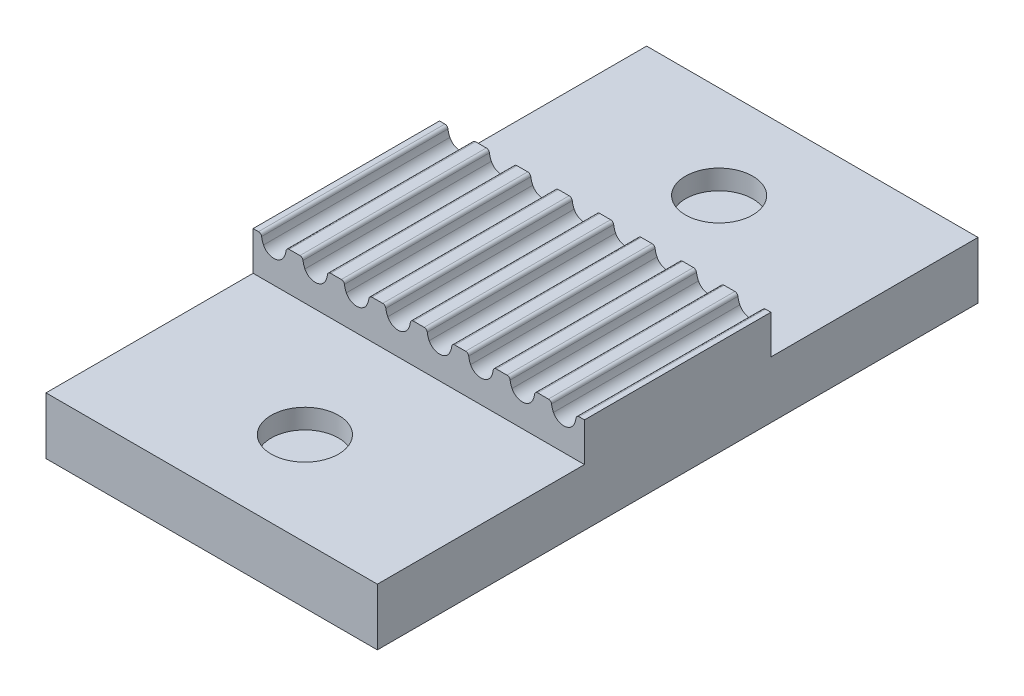
SolidWorks part; units mm, degrees
ref_plane "Front Plane" through (0, 0, 0) normal (0, 0, 1) x (1, 0, 0)
ref_plane "Top Plane" through (0, 0, 0) normal (0, 1, 0) x (1, 0, 0)
ref_plane "Right Plane" through (0, 0, 0) normal (1, 0, 0) x (0, 0, -1)
sketch "Sketch1" plane through (0, 0, 0) normal (0, 0, 1) x (1, 0, 0)
  line L0 (16.338, 17.8213) -> (16.5978, 17.8213)
  line L1 (12.338, 17.8213) -> (12.8577, 17.8213)
  line L2 (14.338, 17.8213) -> (14.8577, 17.8213)
  line L3 (8.338, 17.8213) -> (8.8577, 17.8213)
  line L4 (10.338, 17.8213) -> (10.8577, 17.8213)
  line L5 (16.5978, 17.8213) -> (16.5978, 15.9513)
  line L6 (0.5978, 17.8213) -> (0.5978, 15.9513)
  line L7 (4.338, 17.8213) -> (4.8577, 17.8213)
  line L8 (6.338, 17.8213) -> (6.8577, 17.8213)
  line L9 (0.5978, 17.8213) -> (0.8577, 17.8213)
  line L10 (2.338, 17.8213) -> (2.8577, 17.8213)
  line L11 (0.5978, 15.9513) -> (16.5978, 15.9513)
  arc A0 (15.5978, 17.0713) -> (16.0967, 17.3831) centre (15.5978, 17.6263) ccw
  arc A1 (16.0967, 17.3831) -> (16.1893, 17.6909) centre (15.1978, 17.8213) ccw
  arc A2 (16.338, 17.8213) -> (16.1893, 17.6909) centre (16.338, 17.6713) ccw
  arc A3 (13.099, 17.3831) -> (13.5978, 17.0713) centre (13.5978, 17.6263) ccw
  arc A4 (13.0064, 17.6909) -> (13.099, 17.3831) centre (13.9978, 17.8213) ccw
  arc A5 (13.0064, 17.6909) -> (12.8577, 17.8213) centre (12.8577, 17.6713) ccw
  arc A6 (11.5978, 17.0713) -> (12.0967, 17.3831) centre (11.5978, 17.6263) ccw
  arc A7 (12.0967, 17.3831) -> (12.1893, 17.6909) centre (11.1978, 17.8213) ccw
  arc A8 (12.338, 17.8213) -> (12.1893, 17.6909) centre (12.338, 17.6713) ccw
  arc A9 (15.099, 17.3831) -> (15.5978, 17.0713) centre (15.5978, 17.6263) ccw
  arc A10 (15.0064, 17.6909) -> (15.099, 17.3831) centre (15.9978, 17.8213) ccw
  arc A11 (15.0064, 17.6909) -> (14.8577, 17.8213) centre (14.8577, 17.6713) ccw
  arc A12 (13.5978, 17.0713) -> (14.0967, 17.3831) centre (13.5978, 17.6263) ccw
  arc A13 (14.0967, 17.3831) -> (14.1893, 17.6909) centre (13.1978, 17.8213) ccw
  arc A14 (14.338, 17.8213) -> (14.1893, 17.6909) centre (14.338, 17.6713) ccw
  arc A15 (9.099, 17.3831) -> (9.5978, 17.0713) centre (9.5978, 17.6263) ccw
  arc A16 (9.0064, 17.6909) -> (9.099, 17.3831) centre (9.9978, 17.8213) ccw
  arc A17 (9.0064, 17.6909) -> (8.8577, 17.8213) centre (8.8577, 17.6713) ccw
  arc A18 (7.5978, 17.0713) -> (8.0967, 17.3831) centre (7.5978, 17.6263) ccw
  arc A19 (8.0967, 17.3831) -> (8.1893, 17.6909) centre (7.1978, 17.8213) ccw
  arc A20 (8.338, 17.8213) -> (8.1893, 17.6909) centre (8.338, 17.6713) ccw
  arc A21 (11.099, 17.3831) -> (11.5978, 17.0713) centre (11.5978, 17.6263) ccw
  arc A22 (11.0064, 17.6909) -> (11.099, 17.3831) centre (11.9978, 17.8213) ccw
  arc A23 (11.0064, 17.6909) -> (10.8577, 17.8213) centre (10.8577, 17.6713) ccw
  arc A24 (9.5978, 17.0713) -> (10.0967, 17.3831) centre (9.5978, 17.6263) ccw
  arc A25 (10.0967, 17.3831) -> (10.1893, 17.6909) centre (9.1978, 17.8213) ccw
  arc A26 (10.338, 17.8213) -> (10.1893, 17.6909) centre (10.338, 17.6713) ccw
  arc A27 (5.099, 17.3831) -> (5.5978, 17.0713) centre (5.5978, 17.6263) ccw
  arc A28 (5.0064, 17.6909) -> (5.099, 17.3831) centre (5.9978, 17.8213) ccw
  arc A29 (5.0064, 17.6909) -> (4.8577, 17.8213) centre (4.8577, 17.6713) ccw
  arc A30 (3.5978, 17.0713) -> (4.0967, 17.3831) centre (3.5978, 17.6263) ccw
  arc A31 (4.0967, 17.3831) -> (4.1893, 17.6909) centre (3.1978, 17.8213) ccw
  arc A32 (4.338, 17.8213) -> (4.1893, 17.6909) centre (4.338, 17.6713) ccw
  arc A33 (7.099, 17.3831) -> (7.5978, 17.0713) centre (7.5978, 17.6263) ccw
  arc A34 (7.0064, 17.6909) -> (7.099, 17.3831) centre (7.9978, 17.8213) ccw
  arc A35 (7.0064, 17.6909) -> (6.8577, 17.8213) centre (6.8577, 17.6713) ccw
  arc A36 (5.5978, 17.0713) -> (6.0967, 17.3831) centre (5.5978, 17.6263) ccw
  arc A37 (6.0967, 17.3831) -> (6.1893, 17.6909) centre (5.1978, 17.8213) ccw
  arc A38 (6.338, 17.8213) -> (6.1893, 17.6909) centre (6.338, 17.6713) ccw
  arc A39 (1.099, 17.3831) -> (1.5978, 17.0713) centre (1.5978, 17.6263) ccw
  arc A40 (1.0064, 17.6909) -> (1.099, 17.3831) centre (1.9978, 17.8213) ccw
  arc A41 (1.0064, 17.6909) -> (0.8577, 17.8213) centre (0.8577, 17.6713) ccw
  arc A42 (3.099, 17.3831) -> (3.5978, 17.0713) centre (3.5978, 17.6263) ccw
  arc A43 (3.0064, 17.6909) -> (3.099, 17.3831) centre (3.9978, 17.8213) ccw
  arc A44 (3.0064, 17.6909) -> (2.8577, 17.8213) centre (2.8577, 17.6713) ccw
  arc A45 (1.5978, 17.0713) -> (2.0967, 17.3831) centre (1.5978, 17.6263) ccw
  arc A46 (2.0967, 17.3831) -> (2.1893, 17.6909) centre (1.1978, 17.8213) ccw
  arc A47 (2.338, 17.8213) -> (2.1893, 17.6909) centre (2.338, 17.6713) ccw
extrude "Boss-Extrude1" add sketch "Sketch1" along normal blind 9
sketch "Sketch6" plane through (0, 15.9513, 0) normal (0, -1, 0) x (1, 0, 0)
  line L0 (16.5978, 0) -> (0.5978, 0)
  line L1 (0.5978, 0) -> (0.5978, 9)
  line L2 (0.5978, 9) -> (16.5978, 9)
  line L3 (16.5978, 9) -> (16.5978, 0)
extrude "Boss-Extrude6" add sketch "Sketch6" along normal blind 2.75
sketch "Sketch7" plane through (0, 0, 0) normal (0, 0, -1) x (-1, 0, 0)
  line L0 (-16.5978, 13.2013) -> (-0.5978, 13.2013)
  line L1 (-0.5978, 13.2013) -> (-0.5978, 15.9513)
  line L2 (-0.5978, 17.8213) -> (-0.5978, 13.2013) construction
  line L3 (-0.5978, 15.9513) -> (-16.5978, 15.9513)
  line L4 (-16.5978, 13.2013) -> (-16.5978, 17.8213) construction
  line L5 (-16.5978, 15.9513) -> (-16.5978, 13.2013)
extrude "Boss-Extrude7" add sketch "Sketch7" along normal blind 10
sketch "Sketch8" plane through (0, 0, 9) normal (0, 0, 1) x (1, 0, 0)
  line L0 (0.5978, 13.2013) -> (16.5978, 13.2013)
  line L1 (16.5978, 13.2013) -> (16.5978, 15.9513)
  line L2 (16.5978, 13.2013) -> (16.5978, 17.8213) construction
  line L3 (16.5978, 15.9513) -> (0.5978, 15.9513)
  line L4 (0.5978, 17.8213) -> (0.5978, 13.2013) construction
  line L5 (0.5978, 15.9513) -> (0.5978, 13.2013)
extrude "Boss-Extrude8" add sketch "Sketch8" along normal blind 10
sketch "Sketch10" plane through (0, 13.2013, 0) normal (0, -1, 0) x (1, 0, 0)
  line L0 (16.5978, 4.5) -> (0.5978, 4.5) construction
  line L1 (16.5978, -10) -> (16.5978, 19) construction
  line L2 (0.5978, 19) -> (0.5978, -10) construction
  circle A0 centre (8.5978, 14.5) radius 1.625
  circle A1 centre (8.5978, -5.5) radius 1.625
  dimension "D1" = 3.25
  dimension "D3" = 10
  dimension "D2" = 8
extrude "Cut-Extrude1" cut sketch "Sketch10" against normal blind 10
sketch "Sketch11" plane through (0, 13.2013, 0) normal (0, -1, 0) x (1, 0, 0)
  line L0 (0.5978, 19) -> (16.5978, 19) construction
  line L1 (6.938, 11.625) -> (10.2577, 11.625)
  line L2 (10.2577, 11.625) -> (11.9176, 14.5)
  line L3 (11.9176, 14.5) -> (10.2577, 17.375)
  line L4 (10.2577, 17.375) -> (6.938, 17.375)
  line L5 (6.938, 17.375) -> (5.2781, 14.5)
  line L6 (5.2781, 14.5) -> (6.938, 11.625)
  line L7 (0.5978, 4.5) -> (16.5978, 4.5) construction
  line L8 (0.5978, 19) -> (0.5978, -10) construction
  line L9 (16.5978, -10) -> (16.5978, 19) construction
  line L10 (5.2781, -5.5) -> (6.938, -2.625)
  line L11 (6.938, -8.375) -> (5.2781, -5.5)
  line L12 (10.2577, -8.375) -> (6.938, -8.375)
  line L13 (11.9176, -5.5) -> (10.2577, -8.375)
  line L14 (10.2577, -2.625) -> (11.9176, -5.5)
  line L15 (6.938, -2.625) -> (10.2577, -2.625)
  circle A0 centre (8.5978, 14.5) radius 2.875 construction
  circle A1 centre (8.5978, -5.5) radius 2.875 construction
  dimension "D1" = 5.75
extrude "Cut-Extrude2" cut sketch "Sketch11" against normal blind 1.5
sketch "Sketch15" plane through (0, 14.7013, 0) normal (0, -1, 0) x (1, 0, 0)
  line L0 (5.2781, 14.5) -> (6.938, 11.625)
  line L1 (6.938, 11.625) -> (10.2577, 11.625)
  line L2 (6.938, 11.625) -> (10.2577, 11.625) construction
  line L3 (11.9176, 14.5) -> (10.2577, 11.625)
  line L4 (11.9176, 14.5) -> (10.2577, 17.375)
  line L5 (10.2577, 17.375) -> (6.938, 17.375) construction
  line L6 (11.9176, 14.5) -> (10.2577, 17.375) construction
  line L7 (10.2577, 17.375) -> (6.938, 17.375)
  line L8 (6.938, 17.375) -> (5.2781, 14.5)
  line L9 (0.5978, 4.5) -> (16.5978, 4.5) construction
  line L10 (0.5978, 19) -> (0.5978, -10) construction
  line L11 (16.5978, -10) -> (16.5978, 19) construction
  line L12 (6.938, -8.375) -> (5.2781, -5.5)
  line L13 (10.2577, -8.375) -> (6.938, -8.375)
  line L14 (11.9176, -5.5) -> (10.2577, -8.375)
  line L15 (11.9176, -5.5) -> (10.2577, -2.625)
  line L16 (6.938, -2.625) -> (10.2577, -2.625)
  line L17 (5.2781, -5.5) -> (6.938, -2.625)
extrude "Boss-Extrude11" add sketch "Sketch15" against normal blind 0.3
